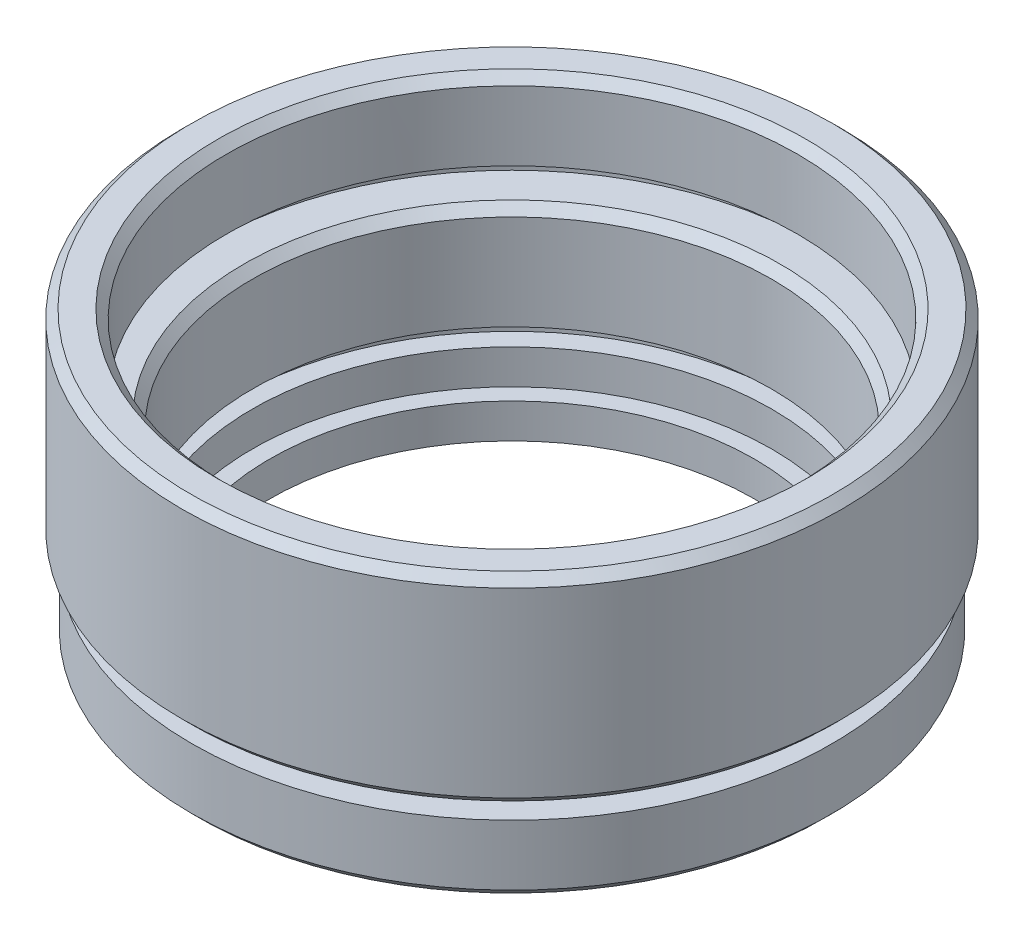
SolidWorks part; units mm, degrees
ref_plane "前视基准面" through (0, 0, 0) normal (0, 0, 1) x (1, 0, 0)
ref_plane "上视基准面" through (0, 0, 0) normal (0, 1, 0) x (1, 0, 0)
ref_plane "右视基准面" through (0, 0, 0) normal (1, 0, 0) x (0, 0, -1)
sketch "草图1" plane through (0, 0, 0) normal (0, 0, 1) x (1, 0, 0)
  line L0 (0, 0) -> (0, 51.3875) construction
  line L1 (14, 0) -> (14, 2)
  line L2 (14, 2) -> (15, 2)
  line L3 (15, 2) -> (15, 4)
  line L4 (15, 4) -> (16.1, 4)
  line L5 (16.1, 4) -> (16.1, 5)
  line L6 (16.1, 5) -> (15, 5)
  line L7 (15, 5) -> (15, 11)
  line L8 (15, 11) -> (17.6, 11)
  line L9 (14, 0) -> (18, 0)
  line L10 (17.6, 11) -> (17.6, 12)
  line L11 (17.6, 12) -> (16.5, 12)
  line L12 (16.5, 12) -> (16.5, 16.5)
  line L13 (16.5, 16.5) -> (18.55, 16.5)
  line L14 (0, 0) -> (5.8539, 0) construction
  line L15 (18.5, 0.5) -> (18.5, 4)
  line L16 (18.5, 4) -> (17, 4)
  line L17 (17, 4) -> (17, 5)
  line L18 (17, 5) -> (18.55, 5)
  line L19 (19.05, 5.5) -> (19.05, 16)
  line L20 (18, 0) -> (18.5, 0.5)
  line L21 (18.55, 5) -> (19.05, 5.5)
  line L22 (19.05, 16) -> (18.55, 16.5)
  point P13 (18.5, 0)
  point P22 (19.05, 5)
  point P24 (19.05, 16.5)
  dimension "D1" = 14
  dimension "D2" = 2
  dimension "D3" = 15
  dimension "D4" = 2
  dimension "D5" = 16.1
  dimension "D6" = 1
  dimension "D7" = 15
  dimension "D8" = 1
  dimension "D9" = 17.6
  dimension "D10" = 5.5
  dimension "D11" = 16.5
  dimension "D12" = 16.5
  dimension "D13" = 18.5
  dimension "D14" = 1
  dimension "D15" = 0.5
  dimension "D16" = 17
  dimension "D17" = 19.05
  dimension "D18" = 0.5
  dimension "D19" = 45
  dimension "D20" = 45
  dimension "D21" = 0.5
  dimension "D22" = 45
  dimension "D23" = 5
revolve "旋转1" add sketch "草图1" angle 360 about L0
cosmetic thread "装饰螺纹线1"
cosmetic thread "装饰螺纹线2"
cosmetic thread "装饰螺纹线3"
chamfer "倒角1" distance 0.5 angle 45 2 edges at (0, 11, -15) (0, 16.5, -16.5)
